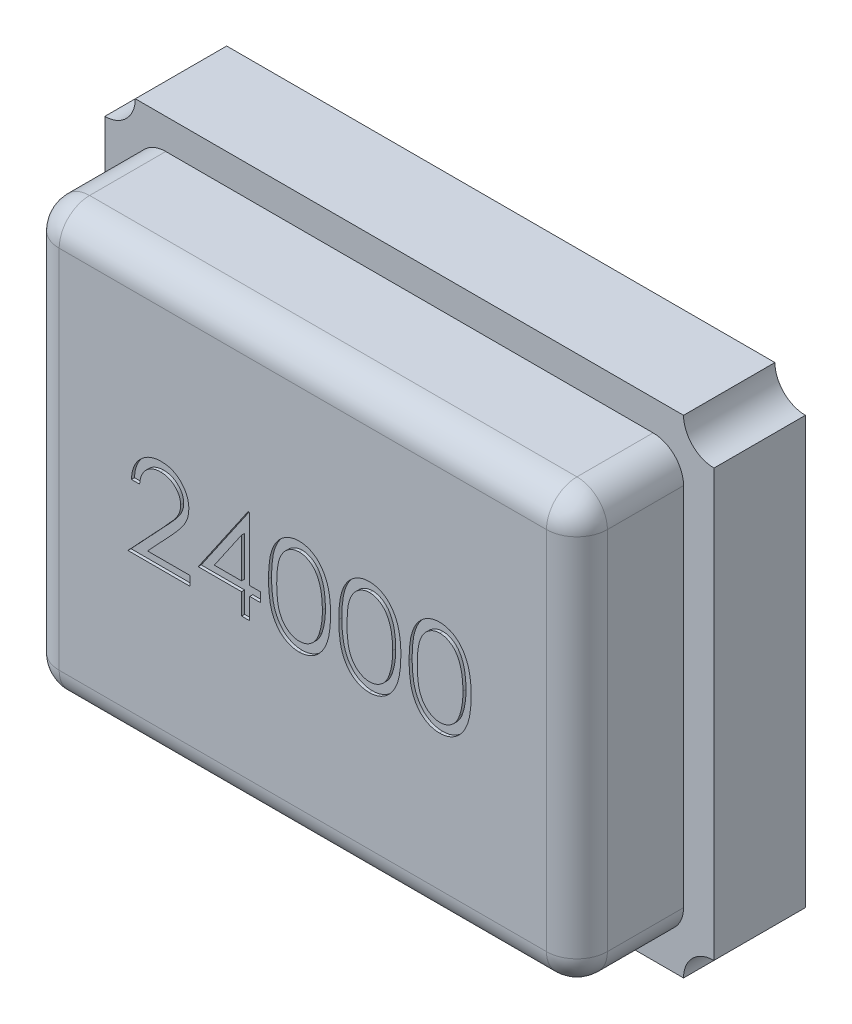
SolidWorks part; units mm, degrees
ref_plane "Спереди" through (0, 0, 0) normal (0, 0, 1) x (1, 0, 0)
ref_plane "Сверху" through (0, 0, 0) normal (0, 1, 0) x (1, 0, 0)
ref_plane "Справа" through (0, 0, 0) normal (1, 0, 0) x (0, 0, -1)
sketch "Эскиз1" plane through (0, 0, 0) normal (0, 0, 1) x (1, 0, 0)
  line L1 (-0.9, 0.8) -> (0.9, 0.8)
  line L2 (-1, 0.7) -> (-1, -0.7)
  line L3 (-0.9, -0.8) -> (0.9, -0.8)
  line L4 (1, 0.7) -> (1, -0.7)
  arc A0 (1, 0.7) -> (0.9, 0.8) centre (1, 0.8) cw
  arc A1 (-1, 0.7) -> (-0.9, 0.8) centre (-1, 0.8) ccw
  arc A2 (-1, -0.7) -> (-0.9, -0.8) centre (-1, -0.8) cw
  arc A3 (0.9, -0.8) -> (1, -0.7) centre (1, -0.8) cw
  point P4 (-1, 0)
  point P6 (0, 0.8)
  point P7 (0, 0)
  point P10 (0, 0)
  point P13 (0, 0)
  point P16 (0, 0)
  point P19 (0, 0)
  point P20 (0, 0)
  point P21 (0, 0)
  point P22 (-1.0584, -0.6174)
  point P23 (0, 0)
  point P24 (0, 0)
  point P25 (0, 0)
  point P26 (0, 0)
  point P27 (0, 0)
  point P28 (0, 0)
  point P29 (0, 0)
  point P30 (0, 0)
  dimension "D3" = 0.1
  dimension "D1" = 2
  dimension "D2" = 1.6
extrude "Бобышка-Вытянуть1" add sketch "Эскиз1" along normal blind 0.3
sketch "Эскиз2" plane through (0, 0, 0.3) normal (0, 0, 1) x (1, 0, 0)
  line L1 (-0.8, 0.7) -> (0.8, 0.7)
  line L2 (-0.9, 0.6) -> (-0.9, -0.6)
  line L3 (-0.8, -0.7) -> (0.8, -0.7)
  line L4 (0.9, 0.6) -> (0.9, -0.6)
  arc A0 (-0.9, -0.6) -> (-0.8, -0.7) centre (-0.8, -0.6) ccw
  arc A1 (0.8, -0.7) -> (0.9, -0.6) centre (0.8, -0.6) ccw
  arc A2 (0.8, 0.7) -> (0.9, 0.6) centre (0.8, 0.6) cw
  arc A3 (-0.8, 0.7) -> (-0.9, 0.6) centre (-0.8, 0.6) ccw
  point P4 (0, 0.7)
  point P6 (-0.9, 0)
  point P9 (-0.9, -0.7)
  point P12 (0.9, -0.7)
  point P17 (-0.9, 0.7)
  dimension "D3" = 0.1
  dimension "D1" = 1.4
  dimension "D2" = 1.8
extrude "Бобышка-Вытянуть2" add sketch "Эскиз2" along normal blind 0.35
fillet "Скругление1" radius 0.1 8 edges at (-0.8707, 0.6707, 0.65) (0, 0.7, 0.65) (0.8707, 0.6707, 0.65) (0.9, 0, 0.65) (0.8707, -0.6707, 0.65) (0, -0.7, 0.65) (-0.8707, -0.6707, 0.65) (-0.9, 0, 0.65)
sketch "Эскиз3" plane through (0, 0, 0) normal (0, 0, -1) x (-1, 0, 0)
  line L0 (-1, 0) -> (1, 0) construction
  line L1 (-0.9, 0.7) -> (-0.4, 0.7)
  line L2 (-0.9, 0.7) -> (-0.9, 0.2)
  line L3 (-0.9, 0.2) -> (-0.4, 0.2)
  line L4 (-0.4, 0.7) -> (-0.4, 0.2)
  line L5 (0.4, 0.7) -> (0.9, 0.7)
  line L6 (0.4, 0.7) -> (0.4, 0.2839)
  line L7 (0.5677, 0.2) -> (0.9, 0.2)
  line L8 (0.9, 0.7) -> (0.9, 0.2)
  line L9 (-0.9, -0.2) -> (-0.5677, -0.2)
  line L10 (-0.9, -0.2) -> (-0.9, -0.7)
  line L11 (-0.9, -0.7) -> (-0.4, -0.7)
  line L12 (-0.4, -0.2839) -> (-0.4, -0.7)
  line L13 (0.4, -0.2) -> (0.9, -0.2)
  line L14 (0.4, -0.2) -> (0.4, -0.7)
  line L15 (0.4, -0.7) -> (0.9, -0.7)
  line L16 (0.9, -0.2) -> (0.9, -0.7)
  line L17 (-1, -0.7) -> (-1, 0.7) construction
  line L18 (1, 0.7) -> (1, -0.7) construction
  line L19 (-0.4, -0.2) -> (0.4, 0.2) construction
  line L20 (-0.9, 0.8) -> (0.9, 0.8) construction
  line L21 (0, 0.8) -> (0, -0.8) construction
  line L22 (0.9, -0.8) -> (-0.9, -0.8) construction
  line L23 (0.4, 0.2839) -> (-0.5677, -0.2)
  line L25 (-0.4, -0.2839) -> (0.5677, 0.2)
  point P16 (-0.9, 0.45)
  point P17 (0.9, 0.45)
  point P18 (-0.9, -0.45)
  point P19 (0.9, -0.45)
  point P20 (-0.65, 0.7)
  point P21 (-0.65, -0.7)
  point P22 (0.65, 0.7)
  point P23 (0.65, -0.7)
  dimension "D1" = 0.5
  dimension "D2" = 0.9
  dimension "D3" = 1.3
  dimension "D4" = 0.15
  dimension "D5" = 0.075
extrude "Бобышка-Вытянуть3" add sketch "Эскиз3" along normal blind 0.01
sketch "Эскиз4" plane through (0, 0, 0.65) normal (0, 0, 1) x (1, 0, 0)
  line L0 (-0.5858, -0.1464) -> (0.6516, -0.1464) construction
  text T0 "24000" font "Century Gothic" height 0.3
extrude "Вырез-Вытянуть1" cut sketch "Эскиз4" against normal blind 0.01
